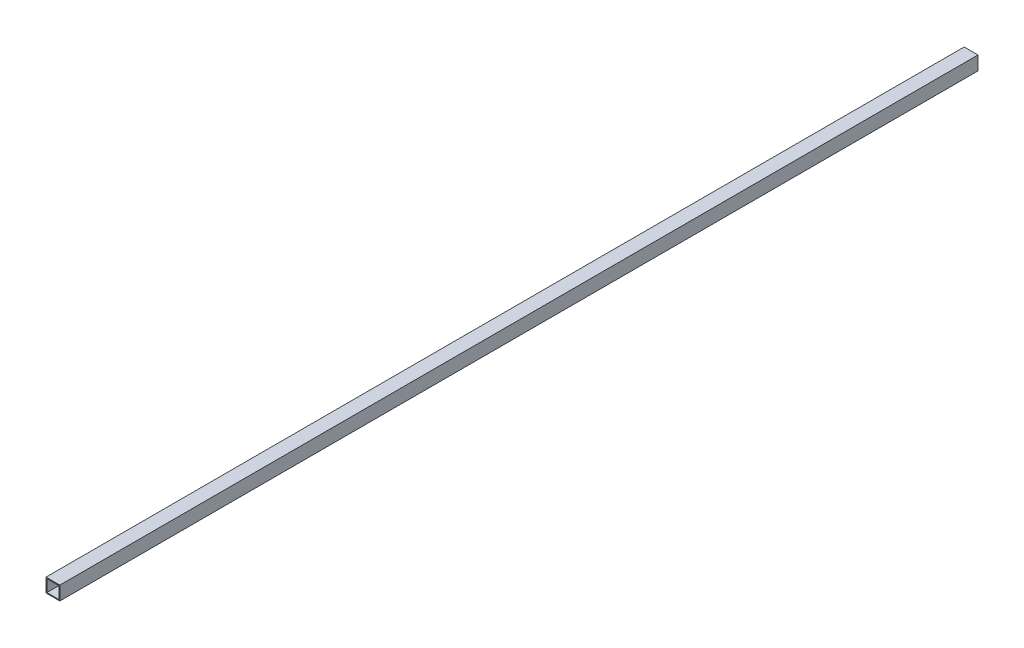
SolidWorks part; units mm, degrees
ref_plane "Front Plane" through (0, 0, 0) normal (0, 0, 1) x (1, 0, 0)
ref_plane "Top Plane" through (0, 0, 0) normal (0, 1, 0) x (1, 0, 0)
ref_plane "Right Plane" through (0, 0, 0) normal (1, 0, 0) x (0, 0, -1)
sketch "Sketch1" plane through (0, 0, 0) normal (0, 0, 1) x (1, 0, 0)
  line L1 (-15, -15) -> (15, -15)
  line L2 (-15, -15) -> (-15, 15)
  line L3 (-15, 15) -> (15, 15)
  line L4 (15, -15) -> (15, 15)
  line L5 (-15, -15) -> (15, 15) construction
  line L6 (-15, 15) -> (15, -15) construction
  line L10 (-13, -13) -> (-13, 13)
  line L11 (-13, 13) -> (13, 13)
  line L12 (13, -13) -> (13, 13)
  line L13 (-13, -13) -> (13, -13)
  point P0 (0, 0)
  dimension "D1" = 30
  dimension "D2" = 30
  dimension "D3" = 2
extrude "Boss-Extrude1" add sketch "Sketch1" along normal mid plane 1992
